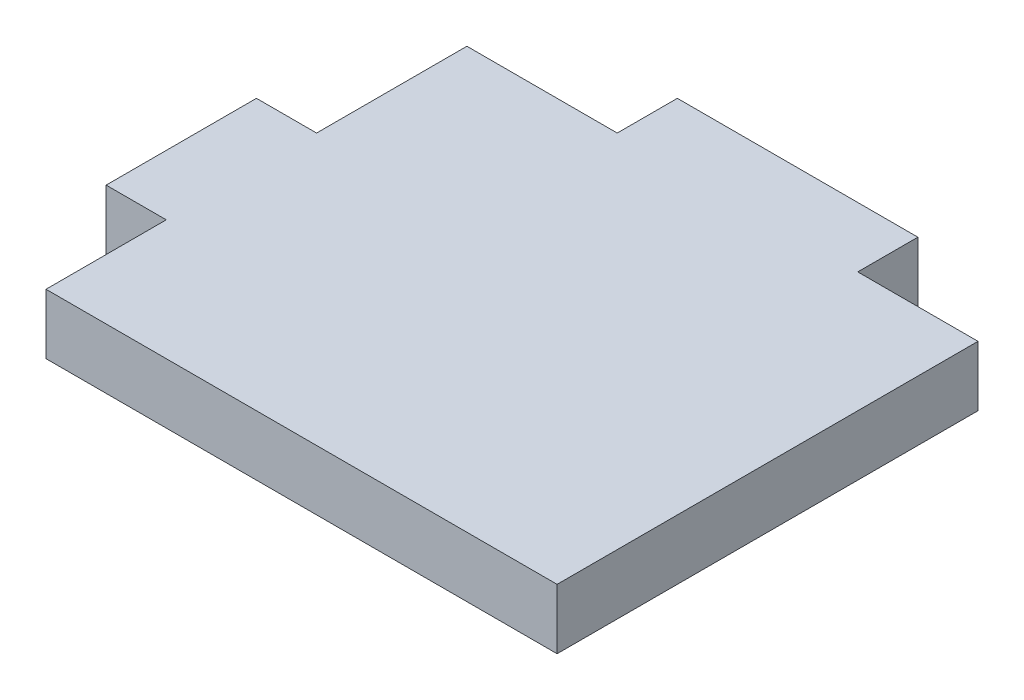
SolidWorks part; units mm, degrees
ref_plane "Front Plane" through (0, 0, 0) normal (0, 0, 1) x (1, 0, 0)
ref_plane "Top Plane" through (0, 0, 0) normal (0, 1, 0) x (1, 0, 0)
ref_plane "Right Plane" through (0, 0, 0) normal (1, 0, 0) x (0, 0, -1)
sketch "Sketch1" plane through (0, 0, 0) normal (0, 1, 0) x (1, 0, 0)
  line L49 (95, 0) -> (10, 0)
  line L53 (95, 0) -> (95, 70)
  line L54 (10, 0) -> (10, 20)
  line L55 (10, 20) -> (0, 20)
  line L56 (0, 20) -> (0, 45)
  line L57 (0, 45) -> (10, 45)
  line L58 (10, 45) -> (10, 70)
  line L59 (10, 70) -> (35, 70)
  line L60 (35, 70) -> (35, 80)
  line L61 (35, 80) -> (75, 80)
  line L62 (75, 80) -> (75, 70)
  line L63 (75, 70) -> (95, 70)
extrude "Boss-Extrude1" add sketch "Sketch1" along normal blind 10
